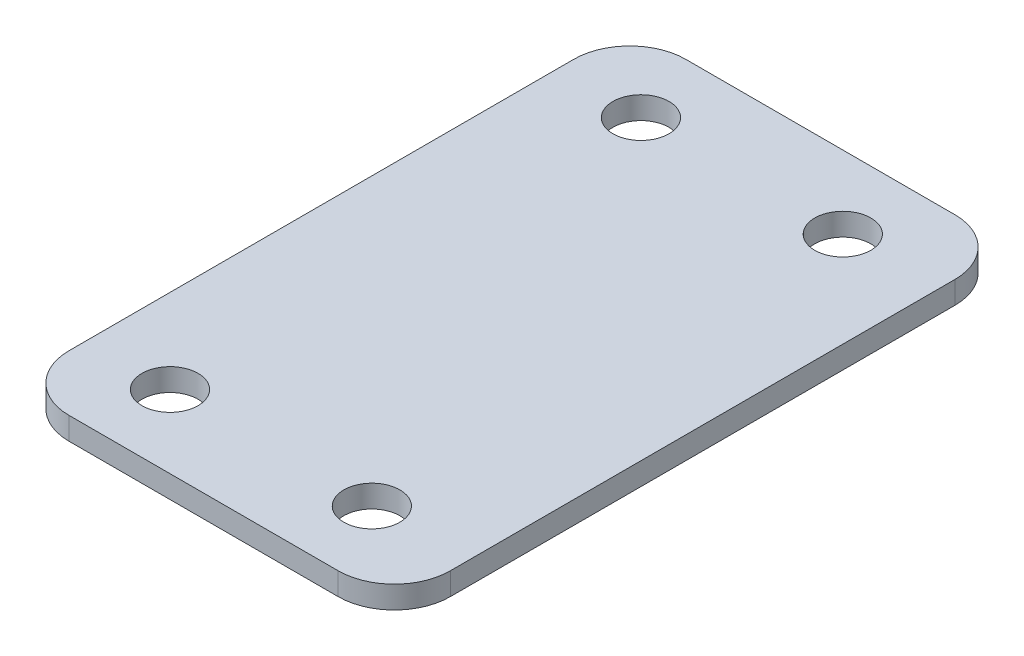
SolidWorks part; units mm, degrees
ref_plane "Front Plane" through (0, 0, 0) normal (0, 0, 1) x (1, 0, 0)
ref_plane "Top Plane" through (0, 0, 0) normal (0, 1, 0) x (1, 0, 0)
ref_plane "Right Plane" through (0, 0, 0) normal (1, 0, 0) x (0, 0, -1)
sketch "Sketch1" plane through (0, 0, 0) normal (0, 1, 0) x (1, 0, 0)
  line L1 (20, -27.5) -> (-20, -27.5)
  line L2 (20, -27.5) -> (20, 27.5)
  line L3 (20, 27.5) -> (-20, 27.5)
  line L4 (-20, -27.5) -> (-20, 27.5)
  line L5 (20, -27.5) -> (-20, 27.5) construction
  line L6 (20, 27.5) -> (-20, -27.5) construction
  point P0 (0, 0)
  dimension "D1" = 55
  dimension "D2" = 40
extrude "Boss-Extrude1" add sketch "Sketch1" along normal blind 2
sketch "Sketch3" plane through (0, 2, 0) normal (0, 1, 0) x (1, 0, 0)
  line L0 (-20, 27.5) -> (-20, -27.5) construction
  circle A0 centre (-12.5, 21) radius 2.5
  circle A2 centre (-12.5, -21) radius 2.5
  circle A3 centre (5.5, 21) radius 2.5
  circle A4 centre (5.5, -21) radius 2.5
  dimension "D1" = 42
  dimension "D2" = 21
  dimension "D3" = 7.5
  dimension "D5" = 18
  dimension "D4" = 2
extrude "Cut-Extrude1" cut sketch "Sketch3" against normal blind 2
sketch "Sketch4" plane through (0, 2, 0) normal (0, 1, 0) x (1, 0, 0)
  line L0 (-20, -27.5) -> (20, -27.5) construction
  line L1 (20, 27.5) -> (14, 27.5)
  line L2 (20, 27.5) -> (20, -27.5)
  line L3 (20, -27.5) -> (14, -27.5)
  line L4 (14, 27.5) -> (14, -27.5)
  dimension "D1" = 6
extrude "Cut-Extrude2" cut sketch "Sketch4" against normal blind 2
fillet "Fillet1" radius 5 4 edges at (-20, 1, -27.5) (14, 1, -27.5) (14, 1, 27.5) (-20, 1, 27.5)
